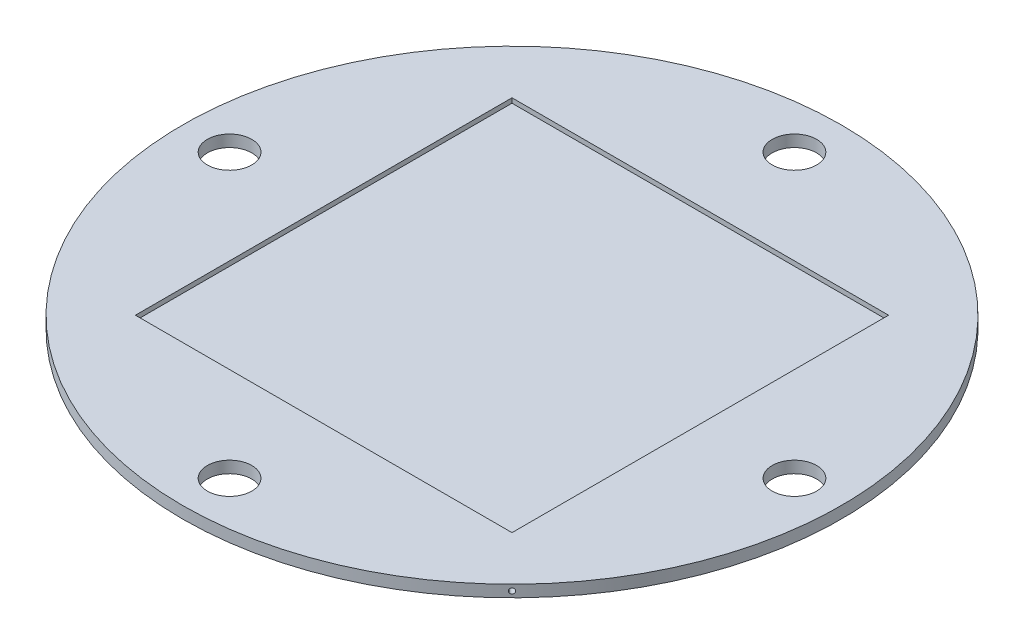
SolidWorks part; units mm, degrees
ref_plane "Front Plane" through (0, 0, 0) normal (0, 0, 1) x (1, 0, 0)
ref_plane "Top Plane" through (0, 0, 0) normal (0, 1, 0) x (1, 0, 0)
ref_plane "Right Plane" through (0, 0, 0) normal (1, 0, 0) x (0, 0, -1)
sketch "Sketch1" plane through (0, 0, 0) normal (0, 1, 0) x (1, 0, 0)
  circle A0 centre (0, 0) radius 88.9
  dimension "D1" = 177.8
extrude "Boss-Extrude1" add sketch "Sketch1" along normal blind 3.175
sketch "Sketch2" plane through (0, 3.175, 0) normal (0, 1, 0) x (1, 0, 0)
  circle A0 centre (0, 76.2) radius 5.9944
  dimension "D1" = 11.9888
  dimension "D2" = 76.2
extrude "Cut-Extrude1" cut sketch "Sketch2" against normal through all
pattern_circular "CirPattern1" count 4 over 360 about axis through (0, 0, 0) along (0, 1, 0) of "Cut-Extrude1"
ref_plane "Plane1" through (-62.8618, 0, 62.8618) normal (-0.7071, 0, 0.7071) x (0, -1, 0)
sketch "Sketch3" plane through (-62.8618, 0, 62.8618) normal (-0.7071, 0, 0.7071) x (0, -1, 0)
  line L0 (0, 0) -> (-3.1494, 0) construction
  circle A0 centre (-1.5875, 0) radius 0.6985
  dimension "D1" = 1.397
  dimension "D2" = 1.5875
extrude "Cut-Extrude2" cut sketch "Sketch3" against normal blind 3.175
pattern_circular "CirPattern2" count 4 over 360 about axis through (0, 0, 0) along (0, 1, 0) of "Cut-Extrude2"
sketch "Sketch4" plane through (0, 3.175, 0) normal (0, 1, 0) x (1, 0, 0)
  line L1 (-50.8, -50.8) -> (50.8, -50.8)
  line L2 (-50.8, -50.8) -> (-50.8, 50.8)
  line L3 (-50.8, 50.8) -> (50.8, 50.8)
  line L4 (50.8, -50.8) -> (50.8, 50.8)
  line L5 (-50.8, -50.8) -> (50.8, 50.8) construction
  line L6 (-50.8, 50.8) -> (50.8, -50.8) construction
  point P0 (0, 0)
  dimension "D1" = 101.6
  dimension "D2" = 101.6
extrude "Cut-Extrude3" cut sketch "Sketch4" against normal blind 1.27
